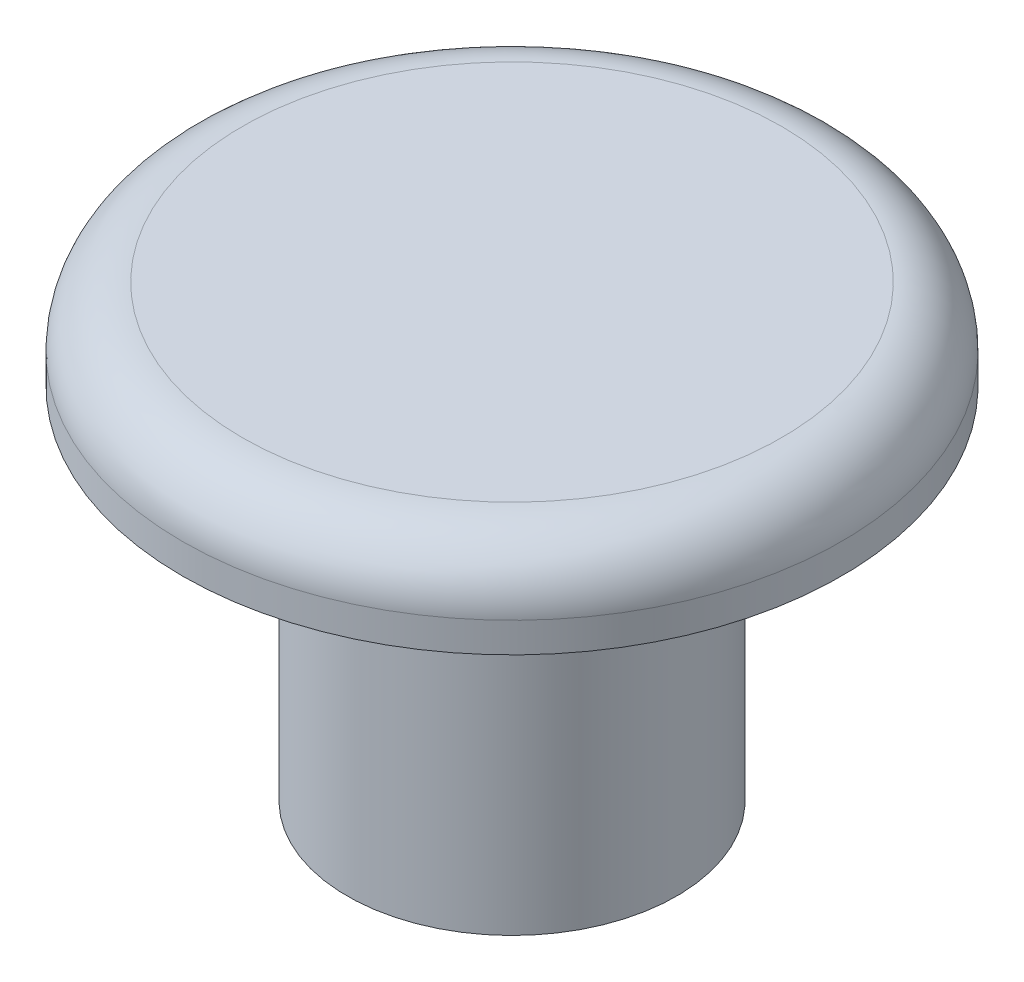
SolidWorks part; units mm, degrees
ref_plane "Front Plane" through (0, 0, 0) normal (0, 0, 1) x (1, 0, 0)
ref_plane "Top Plane" through (0, 0, 0) normal (0, 1, 0) x (1, 0, 0)
ref_plane "Right Plane" through (0, 0, 0) normal (1, 0, 0) x (0, 0, -1)
sketch "Sketch1" plane through (0, 0, 0) normal (0, 1, 0) x (1, 0, 0)
  circle A0 centre (0, 0) radius 11
  dimension "D1" = 22
extrude "Boss-Extrude1" add sketch "Sketch1" along normal blind 3
sketch "Sketch2" plane through (0, 0, 0) normal (0, -1, 0) x (1, 0, 0)
  circle A0 centre (0, 0) radius 5.5
  dimension "D1" = 11
extrude "Boss-Extrude2" add sketch "Sketch2" along normal blind 12
fillet "Fillet1" radius 2 1 edges at (0, 3, 11)
